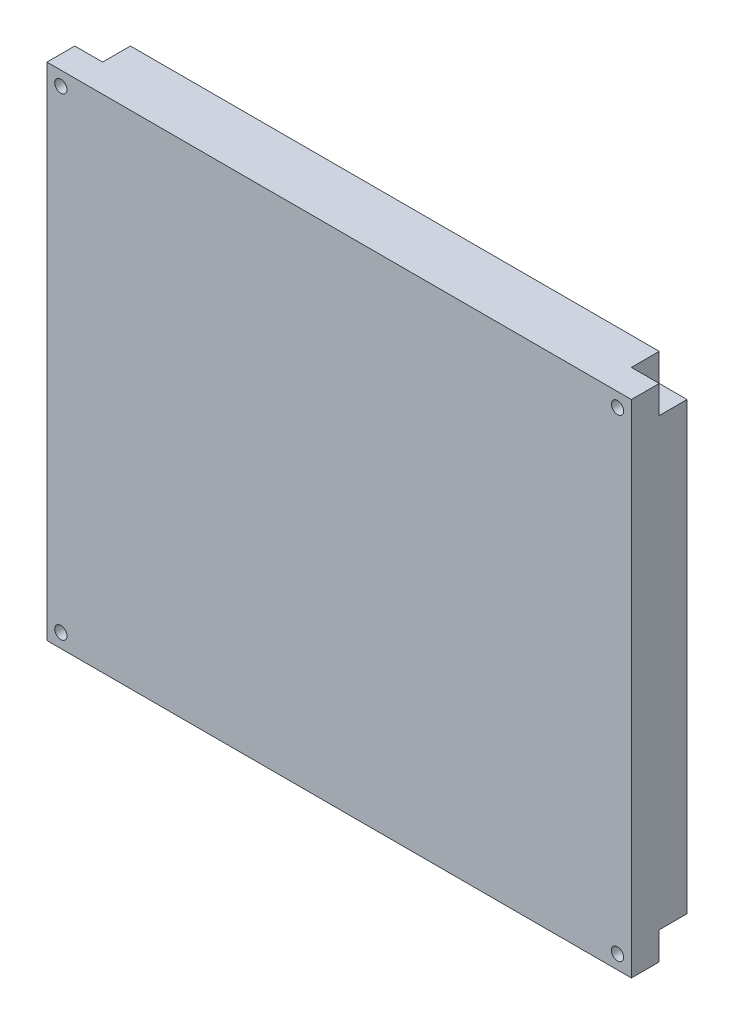
SolidWorks part; units mm, degrees
ref_plane "前基準面" through (0, 0, 0) normal (0, 0, 1) x (1, 0, 0)
ref_plane "上基準面" through (0, 0, 0) normal (0, 1, 0) x (1, 0, 0)
ref_plane "右基準面" through (0, 0, 0) normal (1, 0, 0) x (0, 0, -1)
sketch "草圖1" plane through (0, 0, 0) normal (0, 0, 1) x (1, 0, 0)
  line L1 (-59.0385, 29.8077) -> (45.9615, 29.8077)
  line L2 (-59.0385, 29.8077) -> (-59.0385, -60.1923)
  line L3 (-59.0385, -60.1923) -> (45.9615, -60.1923)
  line L4 (45.9615, 29.8077) -> (45.9615, -60.1923)
  dimension "D1" = 105
  dimension "D2" = 90
extrude "填料-伸長1" add sketch "草圖1" along normal blind 10
sketch "草圖3" plane through (0, 0, 0) normal (0, 0, 1) x (1, 0, 0)
  line L0 (-59.0385, -15.1923) -> (45.9615, -15.1923) construction
  line L1 (-59.0385, 29.8077) -> (-59.0385, -60.1923) construction
  line L2 (45.9615, -60.1923) -> (45.9615, 29.8077) construction
  line L3 (-6.5385, 29.8077) -> (-6.5385, -60.1923) construction
  line L4 (45.9615, 29.8077) -> (-59.0385, 29.8077) construction
  line L5 (-59.0385, -60.1923) -> (45.9615, -60.1923) construction
  line L6 (40.9615, -60.1923) -> (40.9615, -55.1923)
  line L7 (-59.0385, -60.1923) -> (-54.0385, -60.1923)
  line L8 (-59.0385, -60.1923) -> (-59.0385, -55.1923)
  line L9 (-59.0385, -55.1923) -> (-54.0385, -55.1923)
  line L10 (-54.0385, -60.1923) -> (-54.0385, -55.1923)
  line L11 (45.9615, -60.1923) -> (40.9615, -60.1923)
  line L12 (45.9615, -60.1923) -> (45.9615, -55.1923)
  line L13 (45.9615, -55.1923) -> (40.9615, -55.1923)
  line L14 (45.9615, 24.8077) -> (40.9615, 24.8077)
  line L15 (45.9615, 29.8077) -> (45.9615, 24.8077)
  line L16 (45.9615, 29.8077) -> (40.9615, 29.8077)
  line L17 (40.9615, 29.8077) -> (40.9615, 24.8077)
  line L18 (-59.0385, 29.8077) -> (-54.0385, 29.8077)
  line L19 (-59.0385, 29.8077) -> (-59.0385, 24.8077)
  line L20 (-59.0385, 24.8077) -> (-54.0385, 24.8077)
  line L21 (-54.0385, 29.8077) -> (-54.0385, 24.8077)
  dimension "D1" = 5
  dimension "D2" = 5
extrude "除料-伸長1" cut sketch "草圖3" along normal blind 5
sketch "草圖4" plane through (0, 0, 0) normal (0, 0, 1) x (1, 0, 0)
  line L0 (-59.0385, -15.1923) -> (45.9615, -15.1923) construction
  line L1 (-59.0385, 29.8077) -> (-59.0385, -60.1923) construction
  line L2 (45.9615, -60.1923) -> (45.9615, 29.8077) construction
  line L3 (-6.5385, 29.8077) -> (-6.5385, -60.1923) construction
  line L4 (45.9615, 29.8077) -> (-59.0385, 29.8077) construction
  line L5 (-59.0385, -60.1923) -> (45.9615, -60.1923) construction
  line L6 (-59.0385, -57.6923) -> (-54.0385, -57.6923) construction
  line L11 (-56.5385, -55.1923) -> (-56.5385, -60.1923) construction
  circle A0 centre (-56.5385, -57.6923) radius 1.1
  circle A1 centre (43.4615, -57.6923) radius 1.1
  circle A2 centre (43.4615, 27.3077) radius 1.1
  circle A3 centre (-56.5385, 27.3077) radius 1.1
  dimension "D3" = 2.2
extrude "除料-伸長2" cut sketch "草圖4" along normal blind 33.2
